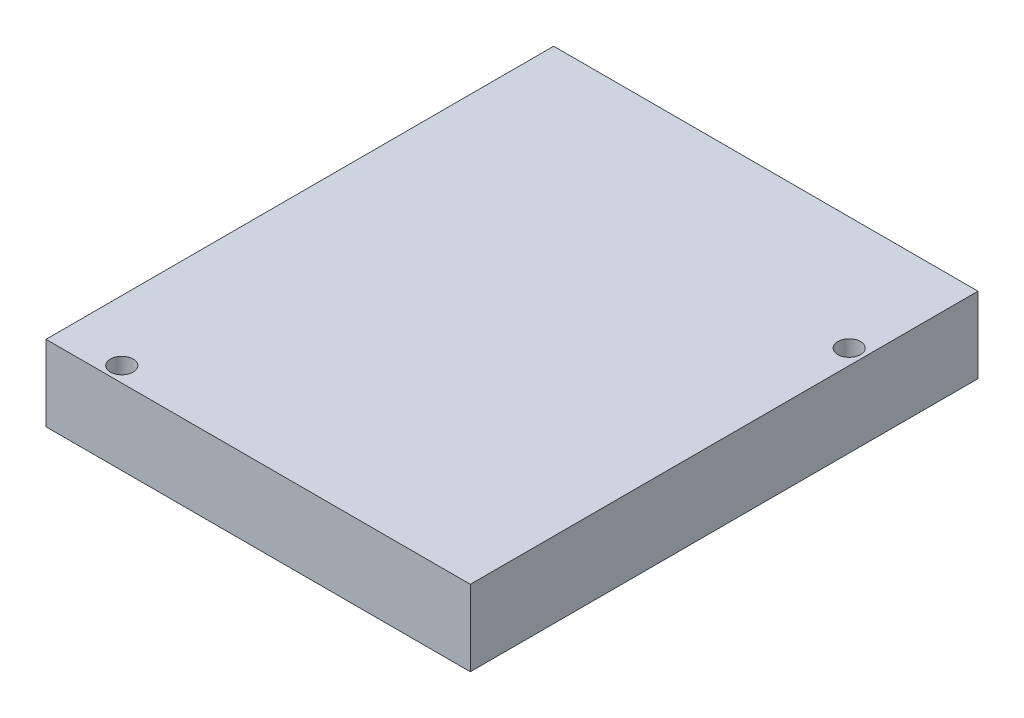
SolidWorks part; units mm, degrees
material "Полиуретановый гибкий пенопласт"
ref_plane "Спереди" through (0, 0, 0) normal (0, 0, 1) x (1, 0, 0)
ref_plane "Сверху" through (0, 0, 0) normal (0, 1, 0) x (1, 0, 0)
ref_plane "Справа" through (0, 0, 0) normal (1, 0, 0) x (0, 0, -1)
sketch "Эскиз1" plane through (0, 0, 0) normal (0, 1, 0) x (1, 0, 0)
  line L0 (0, 33.5) -> (0, -33.5) construction
  line L1 (-28, 33.5) -> (28, 33.5)
  line L2 (-28, 33.5) -> (-28, -33.5)
  line L3 (-28, -33.5) -> (28, -33.5)
  line L4 (28, 33.5) -> (28, -33.5)
  line L5 (-28, 33.5) -> (28, -33.5) construction
  line L6 (-28, -33.5) -> (28, 33.5) construction
  circle A0 centre (26, 18.5) radius 1.5
  circle A1 centre (-20, -31.5) radius 1.5
  point P0 (0, 0)
  dimension "D4" = 20
  dimension "D5" = 3
  dimension "D7" = 50
  dimension "D8" = 3
  dimension "D6" = 26
  dimension "D1" = 67
  dimension "D2" = 56
  dimension "D3" = 15
extrude "Бобышка-Вытянуть1" add sketch "Эскиз1" along normal blind 10
